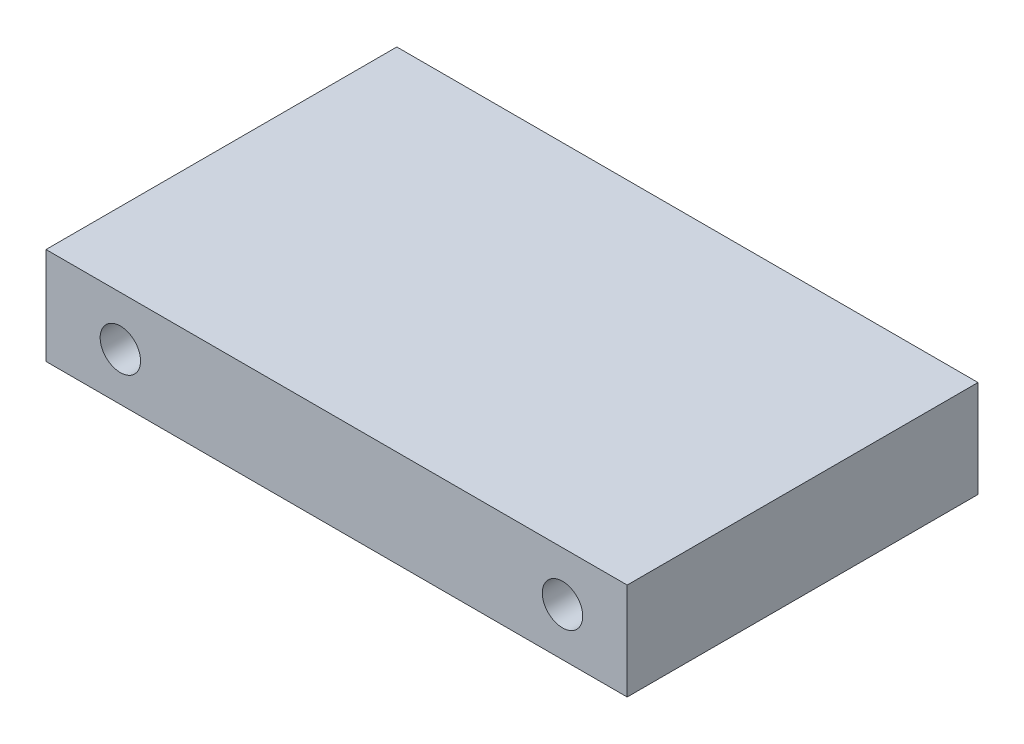
SolidWorks part; units mm, degrees
ref_plane "Ebene vorne" through (0, 0, 0) normal (0, 0, 1) x (1, 0, 0)
ref_plane "Ebene oben" through (0, 0, 0) normal (0, 1, 0) x (1, 0, 0)
ref_plane "Ebene rechts" through (0, 0, 0) normal (1, 0, 0) x (0, 0, -1)
sketch "Side" plane through (0, 0, 0) normal (0, 0, 1) x (1, 0, 0)
  line L1 (-12.6, 570) -> (23.35, 570)
  line L2 (-12.6, 570) -> (-12.6, 564)
  line L3 (-12.6, 564) -> (23.35, 564)
  line L4 (23.35, 570) -> (23.35, 564)
  circle A0 centre (19.35, 566.9539) radius 1.25
  circle A1 centre (-8, 566.9539) radius 1.25
sketch "Skizze3" plane through (0, 0, 0) normal (0, 1, 0) x (1, 0, 0)
  line L1 (-12.6, 12.65) -> (25.15, 12.65)
  line L2 (25.15, 12.65) -> (25.15, -12.65)
  line L3 (25.15, -12.65) -> (-12.6, -12.65)
  line L5 (-12.6, 10.85) -> (23.35, 10.85)
  line L6 (23.35, 10.85) -> (23.35, -10.85)
  line L7 (23.35, -10.85) -> (-12.6, -10.85)
  arc A0 (-12.6, 12.65) -> (-12.6, -12.65) centre (-12.6, 0) ccw
  arc A1 (-12.6, 10.85) -> (-12.6, -10.85) centre (-12.6, 0) ccw
extrude "Aufsatz-Linear austragen1" add sketch "Side" along normal up to vertex (10.85 mm away) and the other way up to vertex (10.85 mm away) up to point (23.35, 0, 10.85) other way up to point (23.35, 0, -10.85)
sketch "Skizze5" plane through (0, 0, 0) normal (0, 0, 1) x (1, 0, 0)
  circle A0 centre (-8, 566.9539) radius 1.25
  circle A1 centre (19.35, 566.9539) radius 1.25
extrude "Schnitt-Linear austragen1" cut sketch "Skizze5" against normal through all both and the other way through all
